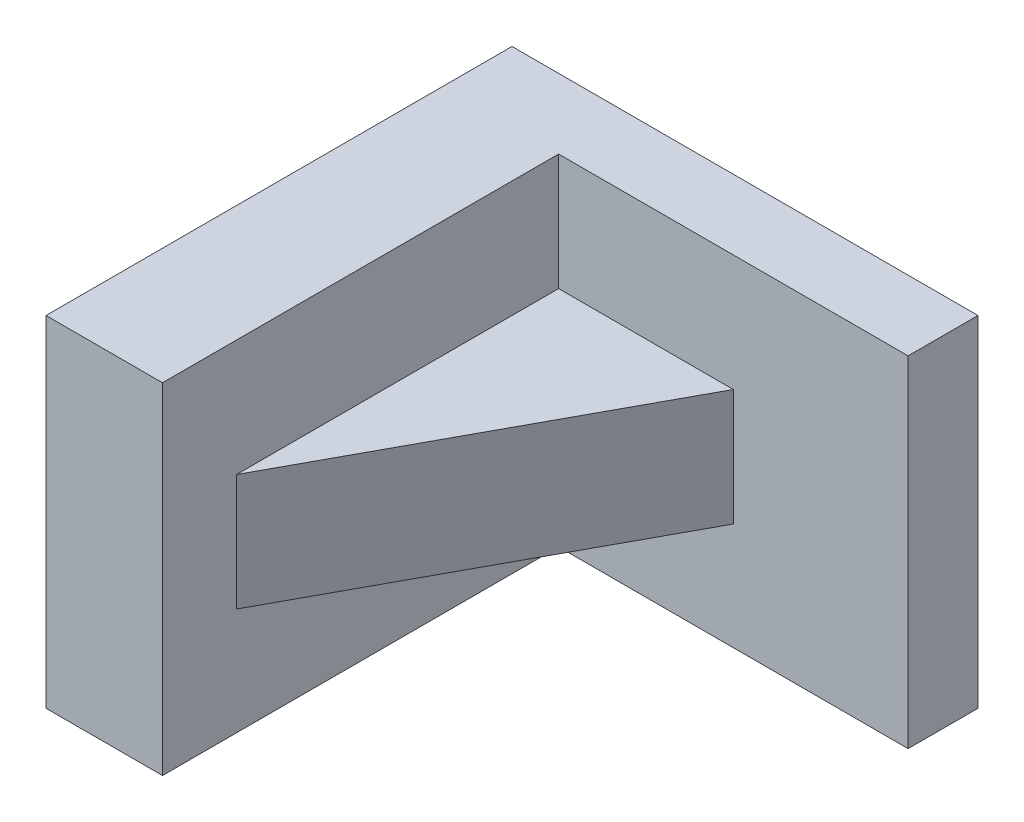
SolidWorks part; units mm, degrees
ref_plane "Front Plane" through (0, 0, 0) normal (0, 0, 1) x (1, 0, 0)
ref_plane "Top Plane" through (0, 0, 0) normal (0, 1, 0) x (1, 0, 0)
ref_plane "Right Plane" through (0, 0, 0) normal (1, 0, 0) x (0, 0, -1)
sketch "Sketch1" plane through (0, 0, 0) normal (0, 1, 0) x (1, 0, 0)
  line L0 (14.3153, 27.7437) -> (-36.4847, 27.7437)
  line L5 (-36.4847, 27.7437) -> (-36.4847, -23.0563)
  line L6 (-36.4847, -23.0563) -> (-23.7847, -23.0563)
  line L7 (-23.7847, -23.0563) -> (-23.7847, 20.1237)
  line L8 (-23.7847, 20.1237) -> (14.3153, 20.1237)
  line L9 (14.3153, 20.1237) -> (14.3153, 27.7437)
  dimension "D1" = 50.8
  dimension "D2" = 50.8
  dimension "D3" = 38.1
  dimension "D4" = 7.62
extrude "Boss-Extrude1" add sketch "Sketch1" along normal blind 37.084
ref_plane "Plane1" through (0, 18.034, 0) normal (0, 1, 0) x (1, 0, 0)
sketch "Sketch4" plane through (0, 18.034, 0) normal (0, 1, 0) x (1, 0, 0)
  line L0 (-23.7847, -14.982) -> (-4.7347, 20.1237)
  line L3 (-23.7847, -23.0563) -> (-23.7847, 20.1237) construction
  line L4 (-4.7347, 20.1237) -> (-23.7847, 20.1237)
  line L5 (-23.7847, 20.1237) -> (14.3153, 20.1237) construction
  line L6 (-23.7847, 20.1237) -> (-23.7847, -14.982)
extrude "Boss-Extrude2" add sketch "Sketch4" along normal mid plane 12.7
